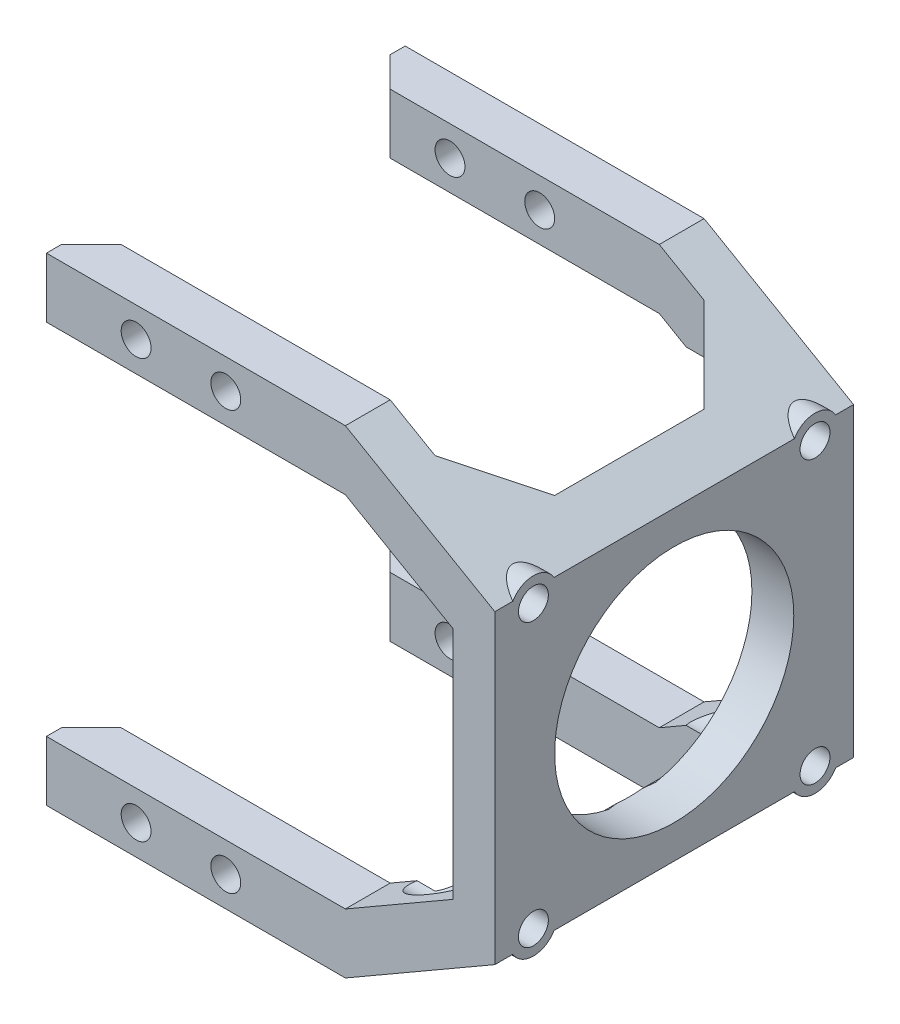
SolidWorks part; units mm, degrees
ref_plane "Front Plane" through (0, 0, 0) normal (0, 0, 1) x (1, 0, 0)
ref_plane "Top Plane" through (0, 0, 0) normal (0, 1, 0) x (1, 0, 0)
ref_plane "Right Plane" through (0, 0, 0) normal (1, 0, 0) x (0, 0, -1)
sketch "Sketch1" plane through (0, 0, 0) normal (0, 0, 1) x (1, 0, 0)
  line L0 (0, 0) -> (25, 14.4338)
  line L1 (25, 14.4338) -> (25, 65.5662)
  line L2 (25, 65.5662) -> (0, 80)
  line L4 (-40, 70) -> (0, 70)
  line L5 (0, 80) -> (-40, 80)
  line L7 (0, 0) -> (-40, 0)
  line L8 (-40, 80) -> (-40, 70)
  line L9 (0, 70) -> (18, 59.6077)
  line L10 (18, 59.6077) -> (18, 20.3923)
  line L11 (18, 20.3923) -> (0, 10)
  line L12 (0, 10) -> (-40, 10)
  line L13 (-40, 10) -> (-40, 0)
  dimension "D1" = 80
  dimension "D2" = 120
  dimension "D3" = 120
  dimension "D5" = 40
  dimension "D6" = 10
  dimension "D7" = 7
  dimension "D8" = 10
extrude "Boss-Extrude1" add sketch "Sketch1" along normal blind 60
sketch "Sketch2" plane through (0, 80, 0) normal (0, 1, 0) x (1, 0, 0)
  line L0 (-40, -60) -> (-40, 0) construction
  line L1 (-97.5, -52.5) -> (17.5, -52.5)
  line L2 (-97.5, -52.5) -> (-97.5, -7.5)
  line L3 (-97.5, -7.5) -> (17.5, -7.5)
  line L4 (17.5, -52.5) -> (17.5, -7.5)
  line L5 (-97.5, -52.5) -> (17.5, -7.5) construction
  line L6 (-97.5, -7.5) -> (17.5, -52.5) construction
  line L7 (25, -60) -> (25, 0) construction
  point P0 (-40, -30)
  dimension "D1" = 45
  dimension "D2" = 7.5
extrude "Cut-Extrude1" cut sketch "Sketch2" against normal through all
sketch "Sketch3" plane through (-40, 0, 0) normal (-1, 0, 0) x (0, 0, 1)
  line L1 (0, 80) -> (7.5, 80)
  line L2 (0, 80) -> (0, 70)
  line L3 (0, 70) -> (7.5, 70)
  line L4 (7.5, 80) -> (7.5, 70)
  line L5 (52.5, 80) -> (60, 80)
  line L6 (52.5, 80) -> (52.5, 70)
  line L7 (52.5, 70) -> (60, 70)
  line L8 (60, 80) -> (60, 70)
  line L9 (52.5, 10) -> (60, 10)
  line L10 (52.5, 10) -> (52.5, 0)
  line L11 (52.5, 0) -> (60, 0)
  line L12 (60, 10) -> (60, 0)
  line L13 (0, 10) -> (7.5, 10)
  line L14 (0, 10) -> (0, 0)
  line L15 (0, 0) -> (7.5, 0)
  line L16 (7.5, 10) -> (7.5, 0)
extrude "Boss-Extrude2" add sketch "Sketch3" along normal blind 10
chamfer "Chamfer1" distance 5 angle 45 4 edges at (-50, 75, 52.5) (-50, 5, 52.5) (-50, 5, 7.5) (-50, 75, 7.5)
sketch "Sketch4" plane through (0, 0, 0) normal (0, 0, -1) x (-1, 0, 0)
  line L0 (0, 80) -> (50, 80) construction
  line L1 (-25, 40) -> (-21.4376, 40) construction
  line L2 (-25, 14.4338) -> (-25, 65.5662) construction
  circle A0 centre (20, 75) radius 2.5
  circle A1 centre (35, 75) radius 2.5
  circle A2 centre (35, 5) radius 2.5
  circle A3 centre (20, 5) radius 2.5
  dimension "D1" = 5
  dimension "D2" = 5
  dimension "D3" = 20
  dimension "D4" = 5
  dimension "D5" = 15
extrude "Cut-Extrude2" cut sketch "Sketch4" against normal through all
chamfer "Chamfer2" distance 10 angle 45 4 edges at (17.5, 15.1036, 52.5) (17.5, 15.1036, 7.5) (17.5, 64.8964, 7.5) (17.5, 64.8964, 52.5)
sketch "Sketch5" plane through (25, 0, 0) normal (1, 0, 0) x (0, 0, -1)
  circle A0 centre (-30, 40) radius 20
  dimension "D1" = 40
extrude "Cut-Extrude3" cut sketch "Sketch5" against normal through all
sketch "Sketch6" plane through (25, 0, 0) normal (1, 0, 0) x (0, 0, -1)
  line L5 (-53.55, 63.55) -> (-6.45, 16.45) construction
  line L6 (-53.55, 16.45) -> (-6.45, 63.55) construction
  circle A0 centre (-53.55, 63.55) radius 2.5
  circle A1 centre (-6.45, 63.55) radius 2.5
  circle A2 centre (-6.45, 16.45) radius 2.5
  circle A3 centre (-53.55, 16.45) radius 2.5
  point P0 (-30, 40)
  point P10 (-30, 40)
  point P13 (-30, 40)
  point P16 (-30, 40)
  point P19 (-30, 40)
  dimension "D3" = 5
  dimension "D1" = 47.1
  dimension "D2" = 47.1
  dimension "D4" = 4
extrude "Cut-Extrude4" cut sketch "Sketch6" against normal through all
sketch "Sketch7" plane through (25, 0, 0) normal (1, 0, 0) x (0, 0, -1)
  circle A0 centre (-53.55, 63.55) radius 2.5
  circle A1 centre (-53.55, 63.55) radius 4
  circle A2 centre (-6.45, 63.55) radius 4
  circle A3 centre (-6.45, 63.55) radius 2.5
  circle A4 centre (-6.45, 16.45) radius 4
  circle A5 centre (-6.45, 16.45) radius 2.5
  circle A6 centre (-53.55, 16.45) radius 4
  circle A7 centre (-53.55, 16.45) radius 2.5
  point P16 (-30, 40)
  dimension "D1" = 8
  dimension "D2" = 4
extrude "Boss-Extrude3" add sketch "Sketch7" against normal blind 5
sketch "Sketch8" plane through (18, 0, 0) normal (-1, 0, 0) x (0, 0, 1)
  circle A0 centre (6.45, 63.55) radius 4
  circle A1 centre (53.55, 63.55) radius 4
  circle A2 centre (53.55, 16.45) radius 4
  circle A3 centre (6.45, 16.45) radius 4
  point P12 (30, 40)
  dimension "D1" = 8
  dimension "D2" = 4
extrude "Cut-Extrude5" cut sketch "Sketch8" along normal through all
